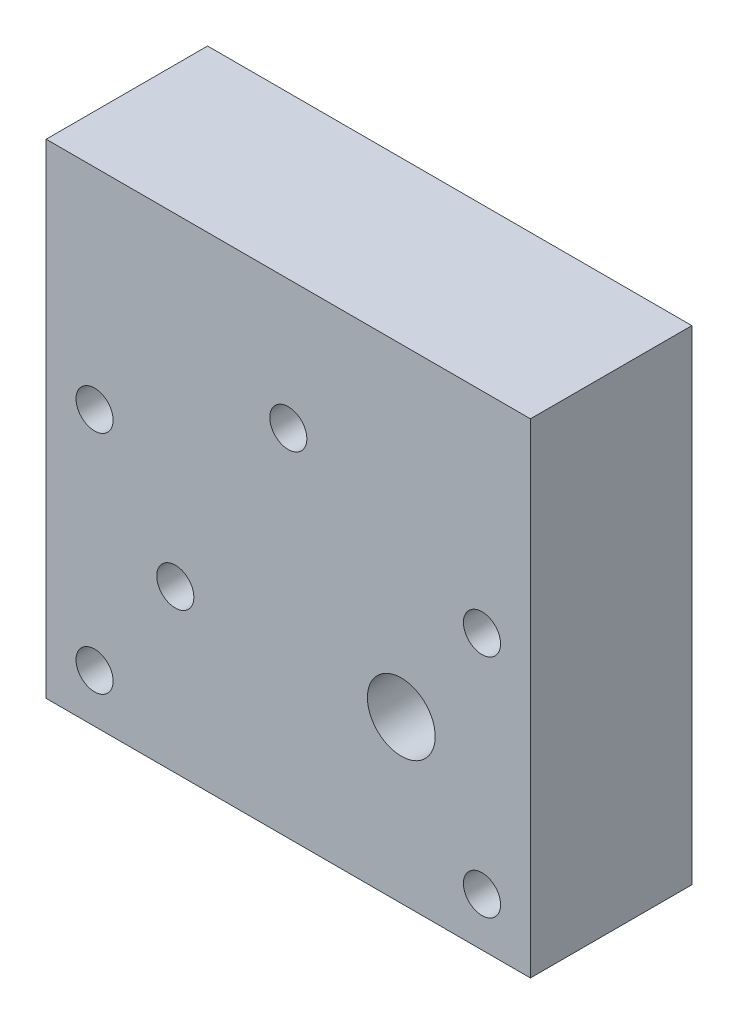
SolidWorks part; units mm, degrees
material "1060 Alloy"
ref_plane "Front Plane" through (0, 0, 0) normal (0, 0, 1) x (1, 0, 0)
ref_plane "Top Plane" through (0, 0, 0) normal (0, 1, 0) x (1, 0, 0)
ref_plane "Right Plane" through (0, 0, 0) normal (1, 0, 0) x (0, 0, -1)
sketch "Sketch1" plane through (0, 0, 0) normal (0, 0, 1) x (1, 0, 0)
  line L1 (0, 0) -> (30, 0)
  line L2 (0, 0) -> (0, 30)
  line L3 (0, 30) -> (30, 30)
  line L4 (30, 0) -> (30, 30)
  circle A0 centre (3, 3) radius 1.15
  circle A1 centre (3, 17) radius 1.15
  circle A2 centre (27, 17) radius 1.15
  circle A3 centre (27, 3) radius 1.15
  circle A4 centre (8, 10) radius 1.15
  circle A5 centre (15, 22) radius 1.15
  circle A6 centre (22, 10) radius 2.1
  dimension "D1" = 3
  dimension "D10" = 2.3
  dimension "D11" = 2.3
  dimension "D12" = 4.2
  dimension "D2" = 3
  dimension "D3" = 14
  dimension "D4" = 3
  dimension "D5" = 8
  dimension "D6" = 15
  dimension "D7" = 8
  dimension "D8" = 30
  dimension "D9" = 30
  dimension "D13" = 10
  dimension "D14" = 22
  dimension "D15" = 10
extrude "Boss-Extrude1" add sketch "Sketch1" along normal blind 10
